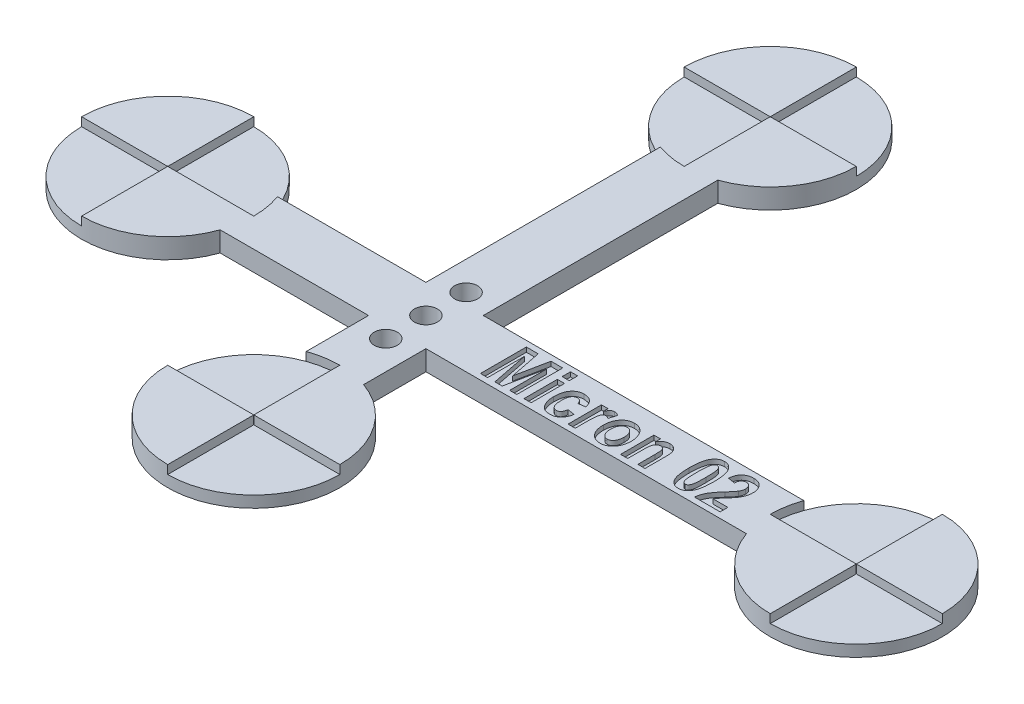
SolidWorks part; units mm, degrees
ref_plane "Front Plane" through (0, 0, 0) normal (0, 0, 1) x (1, 0, 0)
ref_plane "Top Plane" through (0, 0, 0) normal (0, 1, 0) x (1, 0, 0)
ref_plane "Right Plane" through (0, 0, 0) normal (1, 0, 0) x (0, 0, -1)
sketch "Sketch1" plane through (0, 0, 0) normal (0, 1, 0) x (1, 0, 0)
  line L0 (0, 0) -> (120, 0) construction
  line L1 (45, -30) -> (45, 60) construction
  line L2 (40, 45.8579) -> (40, 5)
  line L3 (50, -15.8579) -> (50, -5)
  line L4 (14.1421, 5) -> (40, 5)
  line L5 (105.8579, -5) -> (50, -5)
  line L6 (50, 5) -> (105.8579, 5)
  line L7 (40, -5) -> (40, -15.8579)
  line L8 (40, -5) -> (14.1421, -5)
  line L9 (50, 5) -> (50, 45.8579)
  arc A0 (14.1421, 5) -> (14.1421, -5) centre (0, 0) ccw
  arc A1 (105.8579, -5) -> (105.8579, 5) centre (120, 0) ccw
  arc A2 (50, 45.8579) -> (40, 45.8579) centre (45, 60) ccw
  arc A3 (40, -15.8579) -> (50, -15.8579) centre (45, -30) ccw
  dimension "D1" = 30
  dimension "D3" = 30
  dimension "D5" = 30
  dimension "D6" = 30
  dimension "D2" = 120
  dimension "D4" = 45
  dimension "D7" = 90
  dimension "D8" = 60
  dimension "D9" = 5
  dimension "D10" = 5
  dimension "D11" = 5
  dimension "D12" = 5
extrude "Boss-Extrude1" add sketch "Sketch1" along normal blind 3.5
sketch "Sketch2" plane through (0, 3.5, 0) normal (0, 1, 0) x (1, 0, 0)
  line L0 (-15, 0) -> (-0.05, 0)
  line L1 (45, 75) -> (45, 60.05)
  line L2 (30, 60) -> (44.95, 60)
  line L3 (120, 15) -> (120, 0.05)
  line L4 (0, 15) -> (0, 0.05)
  line L5 (30, -30) -> (44.95, -30)
  line L6 (45.05, 60) -> (60, 60)
  line L7 (45, 59.95) -> (45, 45)
  line L8 (45, -30.05) -> (45, -45)
  line L9 (45.05, -30) -> (60, -30)
  line L10 (0, -0.05) -> (0, -15)
  line L11 (0.05, 0) -> (15, 0)
  line L12 (120, -0.05) -> (120, -15)
  line L13 (120.05, 0) -> (135, 0)
  line L14 (105, 0) -> (119.95, 0)
  line L15 (45, -15) -> (45, -29.95)
  arc A0 (30, 60) -> (45, 45) centre (45, 60) ccw
  arc A1 (-15, 0) -> (0, -15) centre (0, 0) ccw
  arc A2 (45, -45) -> (60, -30) centre (45, -30) ccw
  arc A3 (120, 15) -> (105, 0) centre (120, 0) ccw
  arc A4 (0, 0.05) -> (-0.05, 0) centre (0, 0) ccw
  arc A5 (45, 59.95) -> (45.05, 60) centre (45, 60) ccw
  arc A6 (119.95, 0) -> (120, -0.05) centre (120, 0) ccw
  arc A7 (44.95, -30) -> (45, -30.05) centre (45, -30) ccw
  arc A8 (45, 60.05) -> (44.95, 60) centre (45, 60) ccw
  arc A9 (60, 60) -> (45, 75) centre (45, 60) ccw
  arc A10 (45.05, -30) -> (45, -29.95) centre (45, -30) ccw
  arc A11 (45, -15) -> (30, -30) centre (45, -30) ccw
  arc A12 (0, -0.05) -> (0.05, 0) centre (0, 0) ccw
  arc A13 (15, 0) -> (0, 15) centre (0, 0) ccw
  arc A14 (120.05, 0) -> (120, 0.05) centre (120, 0) ccw
  arc A15 (120, -15) -> (135, 0) centre (120, 0) ccw
  dimension "D1" = 0.1
  dimension "D2" = 0.1
  dimension "D3" = 0.1
  dimension "D4" = 0.1
extrude "Cut-Extrude1" cut sketch "Sketch2" against normal blind 1.5
sketch "Sketch3" plane through (0, 3.5, 0) normal (0, 1, 0) x (1, 0, 0)
  line L0 (55.4289, -4) -> (100.4289, -4) construction
  line L1 (50, -5) -> (105.8579, -5) construction
  text T0 "<b>Micron 02</b>" font "Arial Narrow" height 8
  point P4 (77.9289, -4)
  point P5 (77.9289, -5)
  dimension "D1" = 45
  dimension "D2" = 1
extrude "Cut-Extrude2" cut sketch "Sketch3" against normal blind 0.8
sketch "Sketch4" plane through (0, 3.5, 0) normal (0, 1, 0) x (1, 0, 0)
  line L0 (45, 7) -> (45, -7) construction
  line L1 (0.05, 0) -> (15, 0) construction
  line L2 (45, -29.95) -> (45, -15) construction
  circle A0 centre (45, 0) radius 2
  circle A1 centre (45, 7) radius 2
  circle A2 centre (45, -7) radius 2
  point P4 (45, 0)
  dimension "D1" = 4
  dimension "D3" = 4
  dimension "D4" = 4
  dimension "D2" = 14
extrude "Cut-Extrude3" cut sketch "Sketch4" against normal through all
